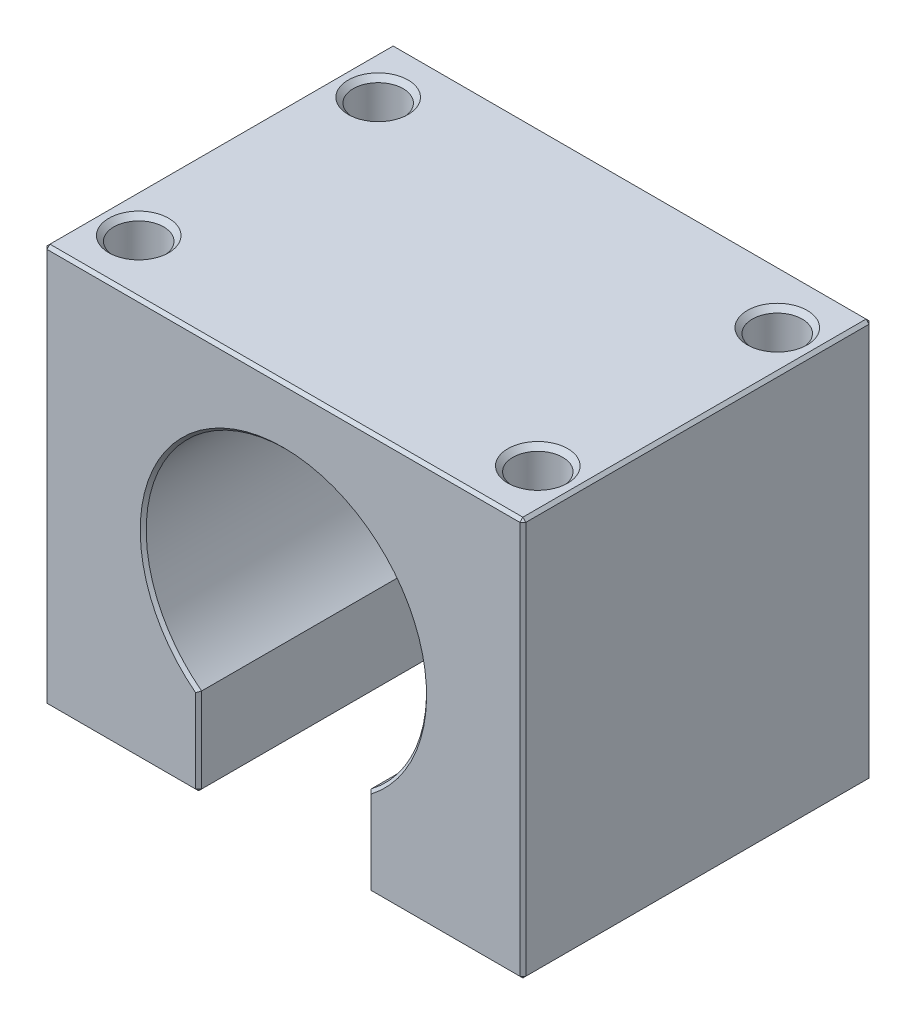
SolidWorks part; units mm, degrees
material "1060 Alloy"
ref_plane "Front Plane" through (0, 0, 0) normal (0, 0, 1) x (1, 0, 0)
ref_plane "Top Plane" through (0, 0, 0) normal (0, 1, 0) x (1, 0, 0)
ref_plane "Right Plane" through (0, 0, 0) normal (1, 0, 0) x (0, 0, -1)
sketch "Sketch1" plane through (0, 0, 0) normal (0, 0, 1) x (1, 0, 0)
  line L0 (-8.5, 0) -> (-8.5, -40) construction
  line L1 (0, 0) -> (-24, 0) construction
  line L2 (0, 0) -> (0, -40) construction
  line L3 (0, -40) -> (-24, -40) construction
  line L4 (-24, 0) -> (-24, -40) construction
  line L5 (-24, -20) -> (-8.5, -20) construction
  line L6 (24, 0) -> (-24, 0)
  line L7 (-24, 0) -> (-24, -40)
  line L8 (-24, -40) -> (-8.5, -40)
  line L9 (-8.5, -40) -> (-8.5, -31.1872)
  line L10 (8.5, -40) -> (8.5, -31.1872)
  line L11 (24, -40) -> (8.5, -40)
  line L12 (24, 0) -> (24, -40)
  circle A0 centre (0, -20) radius 14.05 construction
  arc A1 (8.5, -31.1872) -> (-8.5, -31.1872) centre (0, -20) ccw
  dimension "D5" = 28.1
  dimension "D1" = 24
  dimension "D2" = 40
  dimension "D3" = 8.5
  dimension "D4" = 20
extrude "Boss-Extrude1" add sketch "Sketch1" along normal blind 35
chamfer "Chamfer2" distance 0.3 angle 45 22 edges at (-8.5, -35.5936, 0) (-16.25, -40, 0) (16.25, -40, 0) (8.5, -35.5936, 0) (-24, -20, 0) (-24, -40, 17.5) (8.5, -40, 17.5) (0, 0, 0) (-24, 0, 17.5) (-8.5, -40, 17.5) (-8.5, -35.5936, 35) (-16.25, -40, 35) (-24, -20, 35) (8.5, -35.5936, 35) (16.25, -40, 35) (24, -40, 17.5) (24, -20, 0) (24, 0, 17.5) (0, 0, 35) (24, -20, 35) (0, -5.95, 35) (0, -5.95, 0)
sketch "Sketch2" plane through (0, 0, 0) normal (0, 1, 0) x (1, 0, 0)
  line L0 (0, 0) -> (0, -35) construction
  line L1 (23.7, -35) -> (-23.7, -35) construction
  line L3 (-20, -5.5) -> (20, -5.5) construction
  line L4 (-20, -5.5) -> (-20, -29.5) construction
  line L5 (-20, -29.5) -> (20, -29.5) construction
  line L6 (20, -5.5) -> (20, -29.5) construction
  line L7 (-20, -5.5) -> (20, -29.5) construction
  line L8 (-20, -29.5) -> (20, -5.5) construction
  line L9 (-20, -17.5) -> (20, -17.5) construction
  circle A0 centre (-20, -5.5) radius 2.5
  circle A1 centre (20, -5.5) radius 2.5
  circle A2 centre (20, -29.5) radius 2.5
  circle A3 centre (-20, -29.5) radius 2.5
  point P5 (0, -17.5)
  dimension "D3" = 5
  dimension "D1" = 40
  dimension "D2" = 24
extrude "Cut-Extrude1" cut sketch "Sketch2" against normal blind 17
sketch "Sketch3" plane through (0, 0, 0) normal (0, 0, -1) x (-1, 0, 0)
  line L0 (0, 0) -> (0, -40) construction
  line L1 (0, -20) -> (-20, -40) construction
  line L2 (-24, -20) -> (24, -20) construction
  line L3 (-24, -39.7) -> (-24, -0.3) construction
  line L4 (-8.8, -40) -> (-23.7, -40) construction
  line L5 (0, -20) -> (20, -40) construction
  line L6 (24, -0.3) -> (24, -39.7) construction
  line L7 (-24, -33.435) -> (24, -33.435) construction
  line L8 (-24, -6.565) -> (24, -6.565) construction
  circle A0 centre (0, -20) radius 19 construction
  circle A1 centre (-13.435, -33.435) radius 2.5
  circle A2 centre (13.435, -33.435) radius 2.5
  circle A3 centre (13.435, -6.565) radius 2.5
  circle A4 centre (-13.435, -6.565) radius 2.5
  circle A5 centre (-19, -20) radius 2.5
  circle A6 centre (19, -20) radius 2.5
  dimension "D2" = 38
  dimension "D4" = 5
  dimension "D1" = 40
  dimension "D3" = 45
  dimension "D5" = 13.435
extrude "Cut-Extrude2" cut sketch "Sketch3" against normal blind 20
chamfer "Chamfer3" distance 0.5 angle 45 9 edges at (16.5, -20, 0) (10.935, -33.435, 0) (-10.935, -33.435, 0) (-16.5, -20, 0) (-15.935, -6.565, 0) (17.5, 0, 29.5) (22.5, 0, 5.5) (-17.5, 0, 29.5) (-22.5, 0, 5.5)
